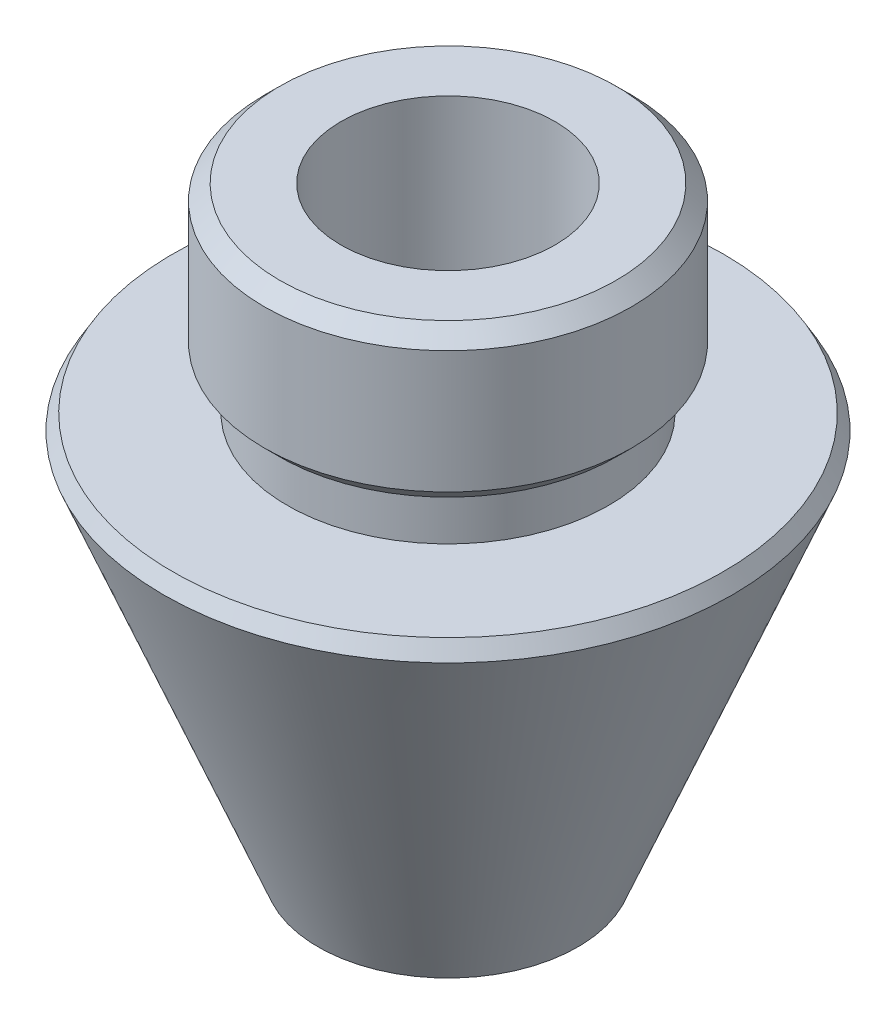
SolidWorks part; units mm, degrees
material "Cobre"
ref_plane "Plano frontal" through (0, 0, 0) normal (0, 0, 1) x (1, 0, 0)
ref_plane "Plano superior" through (0, 0, 0) normal (0, 1, 0) x (1, 0, 0)
ref_plane "Plano direito" through (0, 0, 0) normal (1, 0, 0) x (0, 0, -1)
sketch "Esboço1" plane through (0, 0, 0) normal (1, 0, 0) x (0, 0, -1)
  line L0 (0, 0) -> (0, 40) construction
  line L1 (10.5, 18.7681) -> (19, 18.7681)
  line L2 (19, 18.7681) -> (8.4953, -7.2319)
  line L3 (8.4953, -7.2319) -> (7, -7.2319)
  line L4 (7, 31.7681) -> (7, -7.2319)
  line L5 (-0.5769, 0) -> (1.7552, 0)
  line L6 (10.5, 18.7681) -> (10.5, 21.7681)
  line L7 (10.5, 21.7681) -> (12, 21.7681)
  line L8 (12, 21.7681) -> (12, 31.7681)
  line L9 (12, 31.7681) -> (7, 31.7681)
  line L10 (18, 18.7681) -> (18.5883, 17.7491)
  point P14 (0, 20)
  dimension "D1" = 26
  dimension "D2" = 7
  dimension "D3" = 38
  dimension "D4" = 24
  dimension "D5" = 3
  dimension "D6" = 10
  dimension "D7" = 21
  dimension "D8" = 68
  dimension "D9" = 1
  dimension "D10" = 60
revolve "Revolução1" add sketch "Esboço1" angle 360 about L0
cosmetic thread "Representação de rosca1" parameters "D2"=21.797
chamfer "Chanfro1" distance 1 angle 45 1 edges at (0, 31.7681, -12)
chamfer "Chanfro2" distance 1 angle 45 1 edges at (0, 21.7681, -12)
